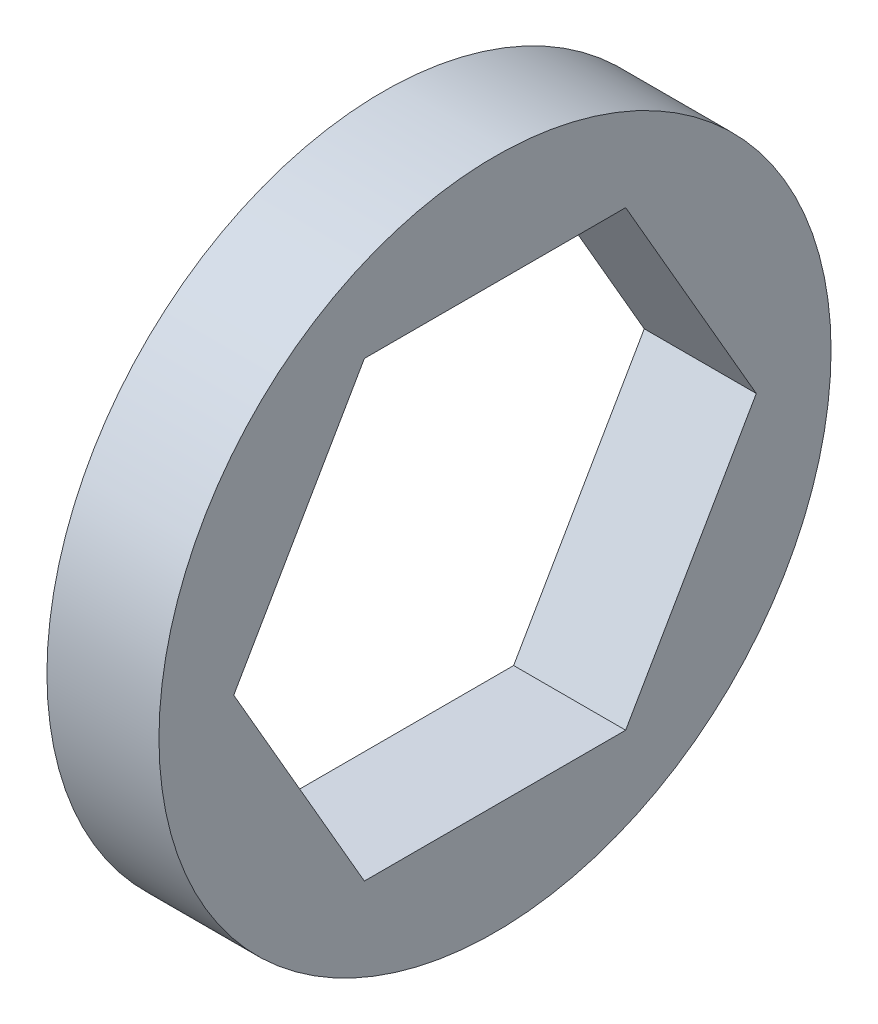
SolidWorks part; units mm, degrees
material "PET"
ref_plane "Front" through (0, 0, 0) normal (0, 0, 1) x (1, 0, 0)
ref_plane "Top" through (0, 0, 0) normal (0, 1, 0) x (1, 0, 0)
ref_plane "Right" through (0, 0, 0) normal (1, 0, 0) x (0, 0, -1)
sketch "Sketch1" plane through (0, 0, 0) normal (1, 0, 0) x (0, 0, -1)
  line L1 (3.7028, 6.4135) -> (-3.7028, 6.4135)
  line L2 (-3.7028, 6.4135) -> (-7.4057, 0)
  line L3 (-7.4057, 0) -> (-3.7028, -6.4135)
  line L4 (-3.7028, -6.4135) -> (3.7028, -6.4135)
  line L5 (3.7028, -6.4135) -> (7.4057, 0)
  line L6 (7.4057, 0) -> (3.7028, 6.4135)
  circle A0 centre (0, 0) radius 9.525
  circle A1 centre (0, 0) radius 6.4135 construction
  dimension "D2" = 19.05
  dimension "D1" = 12.827
extrude "Boss-Extrude1" add sketch "Sketch1" along normal blind 3.175
